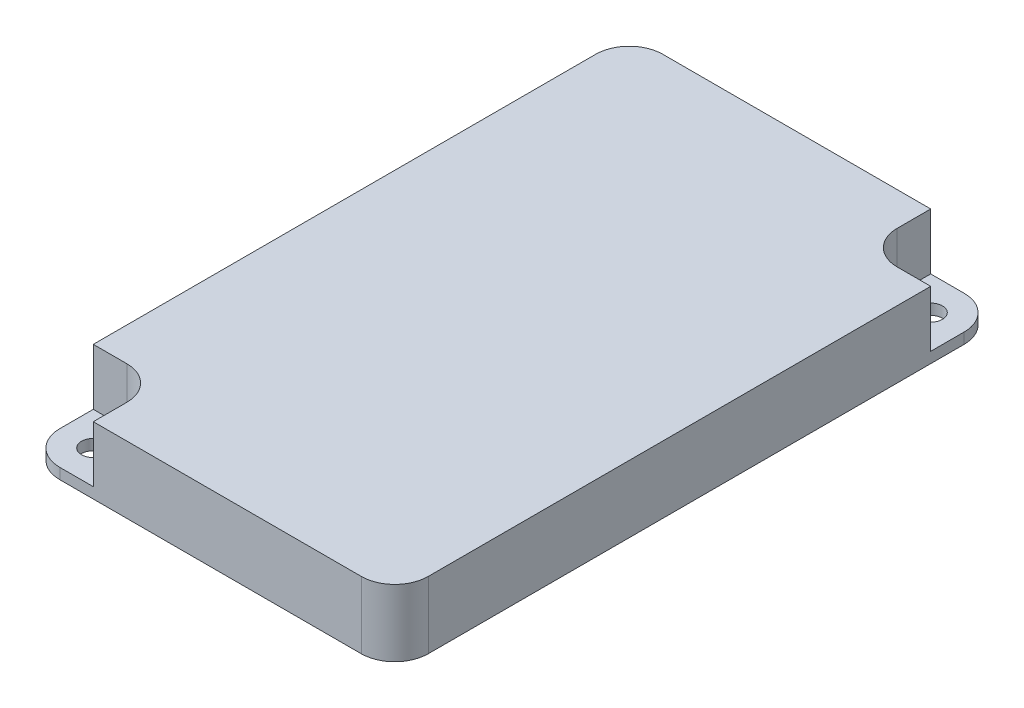
SolidWorks part; units mm, degrees
ref_plane "前视基准面" through (0, 0, 0) normal (0, 0, 1) x (1, 0, 0)
ref_plane "上视基准面" through (0, 0, 0) normal (0, 1, 0) x (1, 0, 0)
ref_plane "右视基准面" through (0, 0, 0) normal (1, 0, 0) x (0, 0, -1)
sketch "草图1" plane through (0, 0, 0) normal (0, 1, 0) x (1, 0, 0)
  line L1 (-22.5, -45) -> (22.5, -45)
  line L2 (-27.5, -40) -> (-27.5, 40)
  line L3 (-22.5, 45) -> (22.5, 45)
  line L4 (27.5, -40) -> (27.5, 40)
  line L5 (-27.5, -45) -> (27.5, 45) construction
  line L6 (-27.5, 45) -> (27.5, -45) construction
  arc A0 (-27.5, 40) -> (-22.5, 45) centre (-22.5, 40) cw
  arc A1 (22.5, 45) -> (27.5, 40) centre (22.5, 40) cw
  arc A2 (22.5, -45) -> (27.5, -40) centre (22.5, -40) ccw
  arc A3 (-22.5, -45) -> (-27.5, -40) centre (-22.5, -40) cw
  circle A4 centre (-22.5, -40) radius 1.75
  circle A6 centre (22.5, 40) radius 1.75
  point P0 (0, 0)
  dimension "D3" = 5
  dimension "D4" = 3.5
  dimension "D5" = 3.5
  dimension "D1" = 55
  dimension "D2" = 90
extrude "凸台-拉伸1" add sketch "草图1" along normal blind 10
sketch "草图2" plane through (0, 10, 0) normal (0, 1, 0) x (1, 0, 0)
  line L0 (-22.5, -35) -> (-27.5, -35)
  line L1 (-27.5, 40) -> (-27.5, -40) construction
  line L2 (-17.5, -40) -> (-17.5, -45)
  line L3 (-22.5, -45) -> (22.5, -45) construction
  line L4 (17.5, 40) -> (17.5, 45)
  line L5 (22.5, 45) -> (-22.5, 45) construction
  line L6 (22.5, 35) -> (27.5, 35)
  line L7 (27.5, -40) -> (27.5, 40) construction
  circle A0 centre (-22.5, -40) radius 5
  circle A1 centre (22.5, 40) radius 5
  line M3 (-27.5, 40) -> (-27.5, -40)
  arc M4 (-27.5, -40) -> (-22.5, -45) centre (-22.5, -40) ccw
  line M5 (-22.5, -45) -> (22.5, -45)
  line M7 (27.5, -40) -> (27.5, 40)
  arc M8 (27.5, 40) -> (22.5, 45) centre (22.5, 40) ccw
  line M9 (22.5, 45) -> (-22.5, 45)
  circle M10 centre (-22.5, -40) radius 1.75
  circle M11 centre (22.5, 40) radius 1.75
extrude "切除-拉伸2" cut sketch "草图2" against normal blind 8.4 contours A1 L4 M9 | A1 M8 M11 | A1 L6 M7 | A0 L0 M3 | A0 M4 M10 | A0 L2 M5
